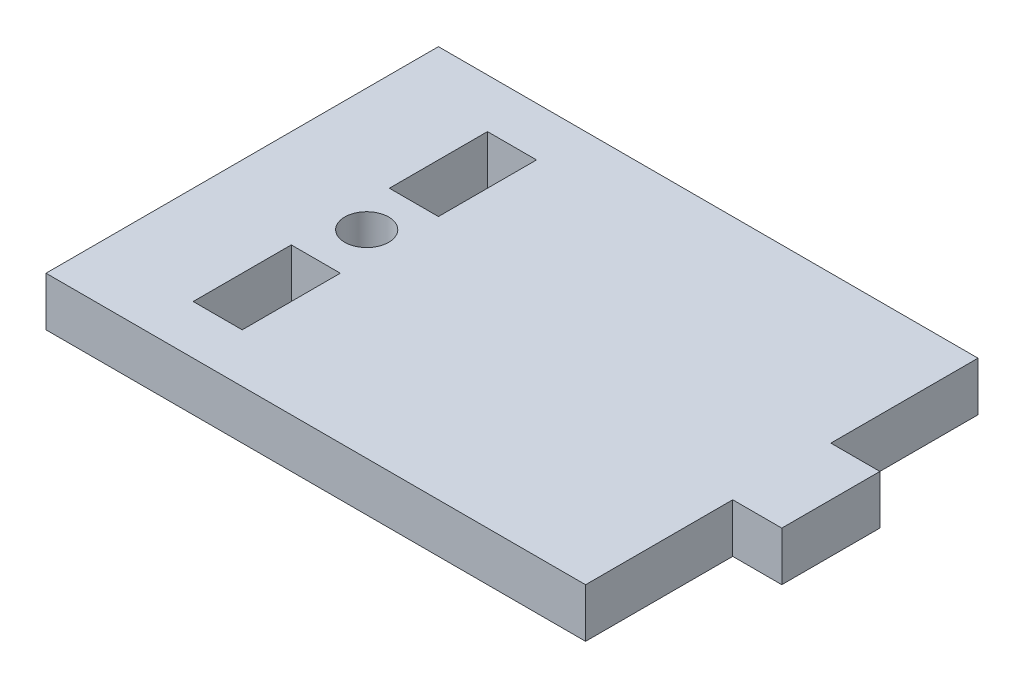
SolidWorks part; units mm, degrees
ref_plane "Front Plane" through (0, 0, 0) normal (0, 0, 1) x (1, 0, 0)
ref_plane "Top Plane" through (0, 0, 0) normal (0, 1, 0) x (1, 0, 0)
ref_plane "Right Plane" through (0, 0, 0) normal (1, 0, 0) x (0, 0, -1)
sketch "Sketch1" plane through (0, 0, 0) normal (0, 1, 0) x (1, 0, 0)
  line L1 (0, 0) -> (69.85, 0)
  line L2 (0, 0) -> (0, 50.8)
  line L3 (0, 50.8) -> (69.85, 50.8)
  line L4 (76.2, 19.05) -> (76.2, 31.75)
  line L5 (12.7, 44.45) -> (19.05, 44.45)
  line L6 (12.7, 44.45) -> (12.7, 31.75)
  line L7 (12.7, 31.75) -> (19.05, 31.75)
  line L8 (19.05, 44.45) -> (19.05, 31.75)
  line L9 (12.7, 19.05) -> (19.05, 19.05)
  line L10 (12.7, 19.05) -> (12.7, 6.35)
  line L11 (12.7, 6.35) -> (19.05, 6.35)
  line L12 (19.05, 19.05) -> (19.05, 6.35)
  line L13 (76.2, 31.75) -> (69.85, 31.75)
  line L16 (69.85, 31.75) -> (69.85, 50.8)
  line L17 (76.2, 19.05) -> (69.85, 19.05)
  line L20 (69.85, 19.05) -> (69.85, 0)
  circle A0 centre (15.875, 25.6404) radius 2.8466
  dimension "D1" = 50.8
  dimension "D3" = 6.35
  dimension "D4" = 6.35
  dimension "D5" = 12.7
  dimension "D6" = 12.7
  dimension "D7" = 15.875
  dimension "D8" = 6.35
  dimension "D9" = 12.7
  dimension "D10" = 12.7
  dimension "D11" = 12.7
  dimension "D12" = 6.35
  dimension "D13" = 6.35
  dimension "D14" = 12.7
extrude "Boss-Extrude1" add sketch "Sketch1" along normal blind 6.35
